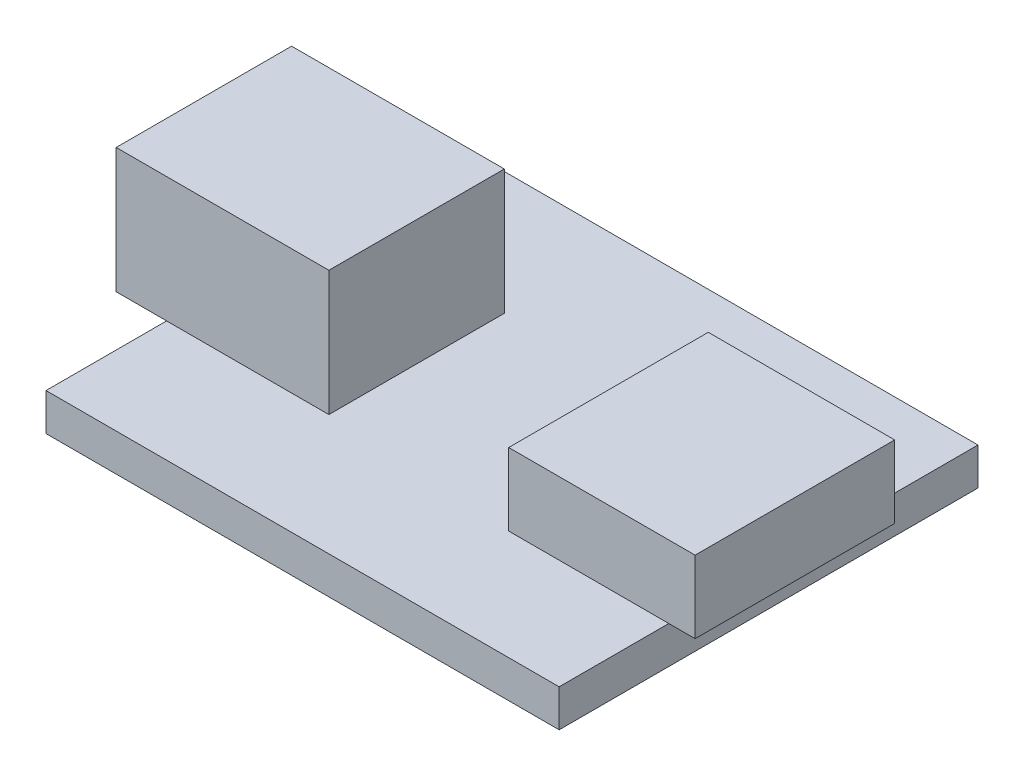
SolidWorks part; units mm, degrees
ref_plane "Front Plane" through (0, 0, 0) normal (0, 0, 1) x (1, 0, 0)
ref_plane "Top Plane" through (0, 0, 0) normal (0, 1, 0) x (1, 0, 0)
ref_plane "Right Plane" through (0, 0, 0) normal (1, 0, 0) x (0, 0, -1)
sketch "Sketch1" plane through (0, 0, 0) normal (0, 1, 0) x (1, 0, 0)
  line L1 (-11.7, 9.55) -> (11.7, 9.55)
  line L2 (-11.7, 9.55) -> (-11.7, -9.55)
  line L3 (-11.7, -9.55) -> (11.7, -9.55)
  line L4 (11.7, 9.55) -> (11.7, -9.55)
  line L5 (-11.7, 9.55) -> (11.7, -9.55) construction
  line L6 (-11.7, -9.55) -> (11.7, 9.55) construction
  point P0 (0, 0)
  dimension "D1" = 19.1
  dimension "D2" = 23.4
extrude "Boss-Extrude1" add sketch "Sketch1" along normal blind 1.7
sketch "Sketch2" plane through (0, 1.7, 0) normal (0, 1, 0) x (1, 0, 0)
  line L0 (11.7, -9.55) -> (11.7, 9.55) construction
  line L1 (4.4, 4.55) -> (11.7, 4.55)
  line L2 (4.4, 4.55) -> (4.4, -4.55)
  line L3 (4.4, -4.55) -> (11.7, -4.55)
  line L4 (11.7, 4.55) -> (11.7, -4.55)
  line L5 (-11.7, -9.55) -> (11.7, -9.55) construction
  line L7 (11.7, 9.55) -> (-11.7, 9.55) construction
  dimension "D1" = 9.1
  dimension "D2" = 7.3
  dimension "D3" = 0
  dimension "D4" = 5
  dimension "D5" = 5
extrude "Boss-Extrude2" add sketch "Sketch2" along normal blind 3.3
sketch "Sketch3" plane through (11.7, 0, 0) normal (1, 0, 0) x (0, 0, -1)
  line L1 (-4.55, 5) -> (4.55, 5)
  line L2 (-4.55, 5) -> (-4.55, 1.7)
  line L3 (-4.55, 1.7) -> (4.55, 1.7)
  line L4 (4.55, 5) -> (4.55, 1.7)
extrude "Boss-Extrude3" add sketch "Sketch3" along normal blind 1.2
sketch "Sketch4" plane through (0, 1.7, 0) normal (0, 1, 0) x (1, 0, 0)
  line L0 (-11.7, 9.55) -> (-11.7, -9.55) construction
  line L1 (-11.7, 3.95) -> (-4.3, 3.95)
  line L2 (-11.7, 3.95) -> (-11.7, -4.05)
  line L3 (-11.7, -4.05) -> (-4.3, -4.05)
  line L4 (-4.3, 3.95) -> (-4.3, -4.05)
  line L5 (-11.7, -9.55) -> (11.7, -9.55) construction
  line L6 (11.7, 9.55) -> (-11.7, 9.55) construction
  dimension "D1" = 8
  dimension "D2" = 7.4
  dimension "D3" = 0
  dimension "D4" = 5.5
  dimension "D5" = 5.6
extrude "Boss-Extrude5" add sketch "Sketch4" along normal blind 5.7
sketch "Sketch5" plane through (-11.7, 0, 0) normal (-1, 0, 0) x (0, 0, 1)
  line L1 (-3.95, 7.4) -> (4.05, 7.4)
  line L2 (-3.95, 7.4) -> (-3.95, 1.7)
  line L3 (-3.95, 1.7) -> (4.05, 1.7)
  line L4 (4.05, 7.4) -> (4.05, 1.7)
extrude "Boss-Extrude6" add sketch "Sketch5" along normal blind 2.3
